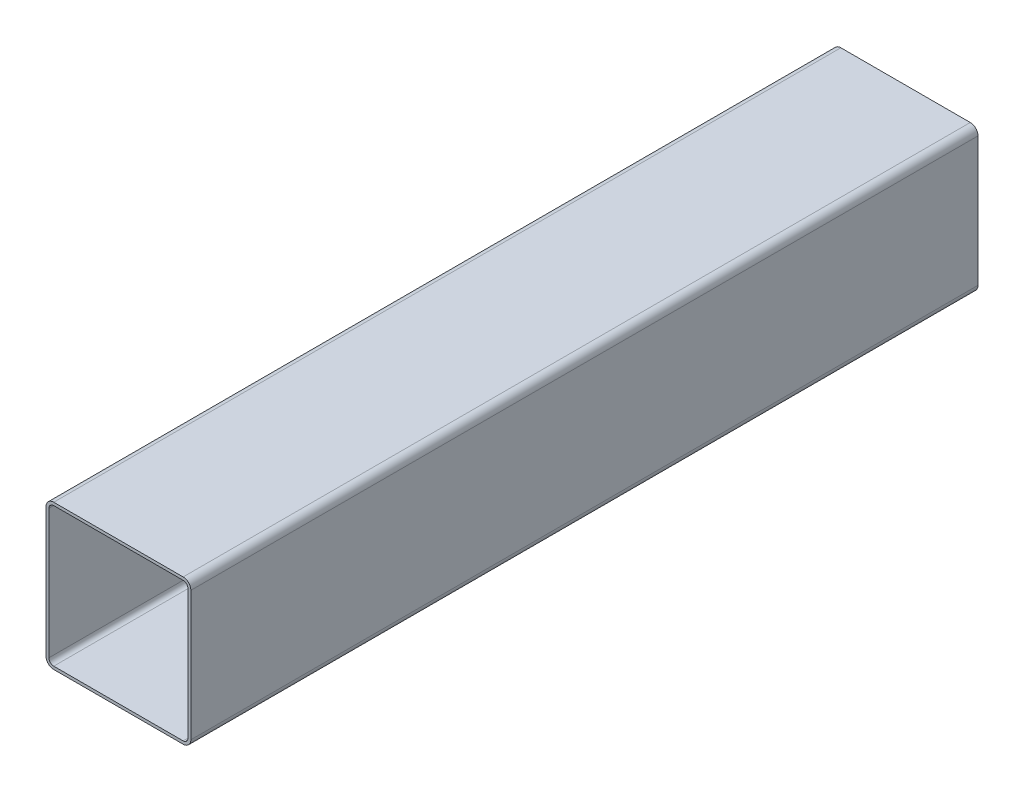
SolidWorks part; units mm, degrees
ref_plane "Спереди" through (0, 0, 0) normal (0, 0, 1) x (1, 0, 0)
ref_plane "Сверху" through (0, 0, 0) normal (0, 1, 0) x (1, 0, 0)
ref_plane "Справа" through (0, 0, 0) normal (1, 0, 0) x (0, 0, -1)
sketch "Эскиз1" plane through (0, 0, 0) normal (0, 0, 1) x (1, 0, 0)
  line L1 (67, -75) -> (-67, -75)
  line L2 (75, -67) -> (75, 67)
  line L3 (67, 75) -> (-67, 75)
  line L4 (-75, -67) -> (-75, 67)
  line L5 (75, -75) -> (-75, 75) construction
  line L6 (75, 75) -> (-75, -75) construction
  arc A0 (-75, -67) -> (-67, -75) centre (-67, -67) ccw
  arc A1 (67, -75) -> (75, -67) centre (67, -67) ccw
  arc A2 (75, 67) -> (67, 75) centre (67, 67) ccw
  arc A3 (-75, 67) -> (-67, 75) centre (-67, 67) cw
  point P0 (0, 0)
  dimension "D2" = 8
  dimension "D1" = 150
extrude "Вытянуть-Тонкостенный1" add sketch "Эскиз1" along normal blind 815 thin
